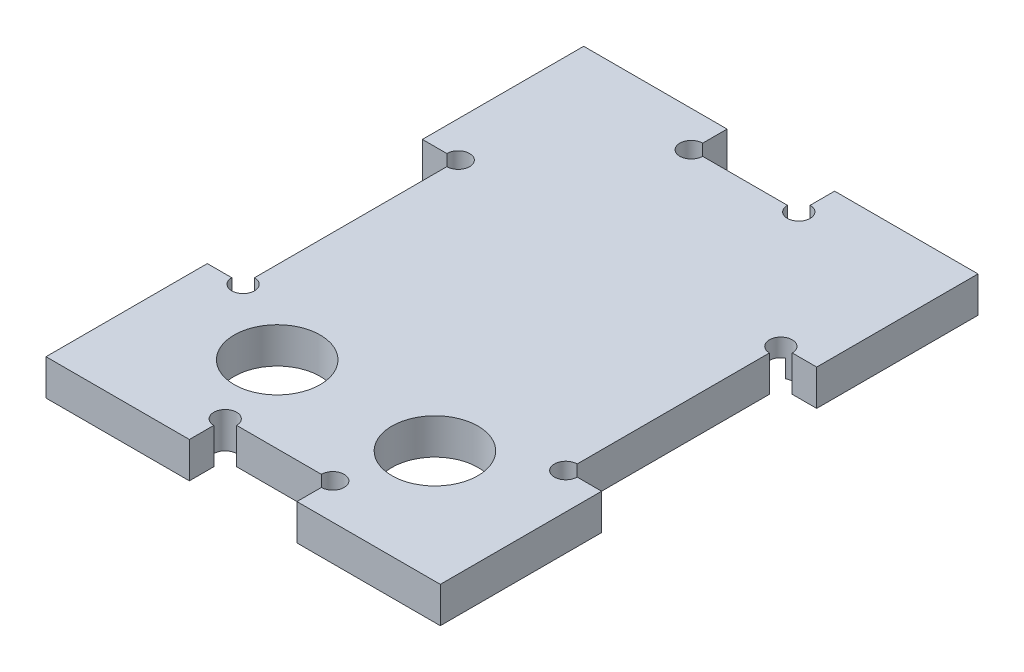
SolidWorks part; units mm, degrees
material "Acrylic (Medium-high impact)"
ref_plane "Front Plane" through (0, 0, 0) normal (0, 0, 1) x (1, 0, 0)
ref_plane "Top Plane" through (0, 0, 0) normal (0, 1, 0) x (1, 0, 0)
ref_plane "Right Plane" through (0, 0, 0) normal (1, 0, 0) x (0, 0, -1)
sketch "Sketch1" plane through (0, 0, 0) normal (0, 1, 0) x (1, 0, 0)
  line L1 (0, 0) -> (55, 0)
  line L2 (0, 0) -> (0, 75)
  line L3 (0, 75) -> (55, 75)
  line L4 (55, 0) -> (55, 75)
  dimension "D1" = 75
  dimension "D2" = 55
extrude "Boss-Extrude1" add sketch "Sketch1" along normal blind 5
sketch "Sketch5" plane through (0, 5, 0) normal (0, 1, 0) x (1, 0, 0)
  line L0 (0, 75) -> (0, 0) construction
  line L1 (0, 22.5) -> (5, 22.5)
  line L2 (0, 22.5) -> (0, 52.5)
  line L3 (0, 52.5) -> (5, 52.5)
  line L4 (5, 22.5) -> (5, 52.5)
  line L5 (55, 75) -> (0, 75) construction
  line L6 (35, 75) -> (20, 75)
  line L7 (35, 75) -> (35, 70)
  line L8 (35, 70) -> (20, 70)
  line L9 (20, 75) -> (20, 70)
  line L10 (55, 0) -> (55, 75) construction
  line L11 (55, 52.5) -> (50, 52.5)
  line L12 (55, 52.5) -> (55, 22.5)
  line L13 (55, 22.5) -> (50, 22.5)
  line L14 (50, 52.5) -> (50, 22.5)
  line L15 (0, 0) -> (55, 0) construction
  line L16 (20, 0) -> (35, 0)
  line L17 (20, 0) -> (20, 5)
  line L18 (20, 5) -> (35, 5)
  line L19 (35, 0) -> (35, 5)
  point P25 (0, 37.5)
  point P26 (27.5, 0)
  dimension "D1" = 5
  dimension "D2" = 30
  dimension "D3" = 15
extrude "Cut-Extrude3" cut sketch "Sketch5" against normal through all both and the other way through all
sketch "Sketch6" plane through (0, 0, 0) normal (0, -1, 0) x (1, 0, 0)
  line L0 (27.5, -5) -> (27.5, -70) construction
  line L1 (7.3375, -70) -> (47.6625, -70)
  line L2 (5.75, -68.4125) -> (5.75, -28.0875)
  line L3 (7.3375, -26.5) -> (47.6625, -26.5)
  line L4 (49.25, -68.4125) -> (49.25, -28.0875)
  line L5 (5.75, -70) -> (49.25, -26.5) construction
  line L6 (5.75, -26.5) -> (49.25, -70) construction
  line L8 (20, -70) -> (35, -70) construction
  arc A0 (49.25, -28.0875) -> (47.6625, -26.5) centre (47.6625, -28.0875) ccw
  arc A1 (49.25, -68.4125) -> (47.6625, -70) centre (47.6625, -68.4125) cw
  arc A2 (7.3375, -70) -> (5.75, -68.4125) centre (7.3375, -68.4125) cw
  arc A3 (5.75, -28.0875) -> (7.3375, -26.5) centre (7.3375, -28.0875) cw
  point P0 (27.5, -48.25)
  dimension "D2" = 1.5875
  dimension "D1" = 43.5
extrude "Cut-Extrude4" cut sketch "Sketch6" against normal blind 2.5
sketch "Sketch7" plane through (0, 5, 0) normal (0, 1, 0) x (1, 0, 0)
  line L0 (27.5, 5) -> (27.5, 26.5) construction
  line L2 (47.6625, 26.5) -> (7.3375, 26.5) construction
  line L3 (20, 5) -> (35, 5) construction
  line L4 (16.5, 15.75) -> (38.5, 15.75) construction
  circle A0 centre (16.5, 15.75) radius 6
  circle A1 centre (38.5, 15.75) radius 6
  point P4 (27.5, 15.75)
  dimension "D1" = 12
  dimension "D2" = 22
extrude "Cut-Extrude5" cut sketch "Sketch7" against normal through all
sketch "Sketch8" plane through (0, 0, 0) normal (0, -1, 0) x (1, 0, 0)
  circle A0 centre (5, -22.5) radius 1.59
  circle A1 centre (20, -5) radius 1.59
  circle A2 centre (35, -5) radius 1.59
  circle A3 centre (50, -22.5) radius 1.59
  circle A4 centre (50, -52.5) radius 1.59
  circle A5 centre (35, -70) radius 1.59
  circle A6 centre (20, -70) radius 1.59
  circle A7 centre (5, -52.5) radius 1.59
  point P25 (35.9541, -5)
  dimension "D1" = 3.18
extrude "Cut-Extrude6" cut sketch "Sketch8" against normal through all
equation "\"cortador\"=3.175"
equation "\"D2@Sketch6\"=\"cortador\"/2"
